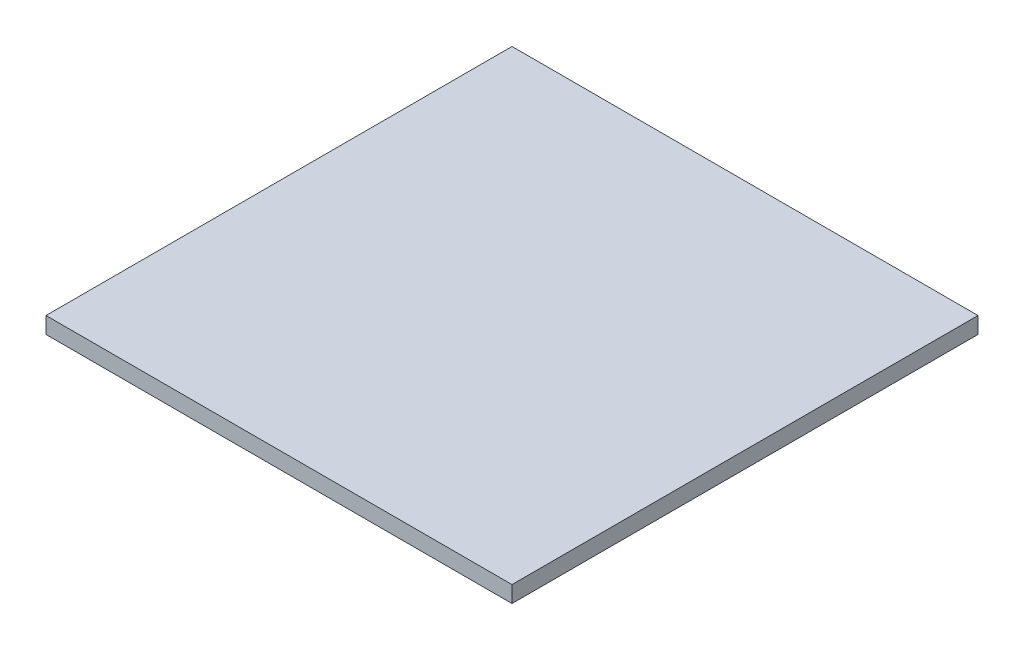
SolidWorks part; units mm, degrees
ref_plane "Front Plane" through (0, 0, 0) normal (0, 0, 1) x (1, 0, 0)
ref_plane "Top Plane" through (0, 0, 0) normal (0, 1, 0) x (1, 0, 0)
ref_plane "Right Plane" through (0, 0, 0) normal (1, 0, 0) x (0, 0, -1)
sketch "Sketch1" plane through (0, 0, 0) normal (0, 1, 0) x (1, 0, 0)
  line L1 (-42.5, -42.5) -> (42.5, -42.5)
  line L2 (-42.5, -42.5) -> (-42.5, 42.5)
  line L3 (-42.5, 42.5) -> (42.5, 42.5)
  line L4 (42.5, -42.5) -> (42.5, 42.5)
  line L5 (-42.5, -42.5) -> (42.5, 42.5) construction
  line L6 (-42.5, 42.5) -> (42.5, -42.5) construction
  point P0 (0, 0)
  dimension "D1" = 85
  dimension "D2" = 85
extrude "Boss-Extrude1" add sketch "Sketch1" along normal blind 3
